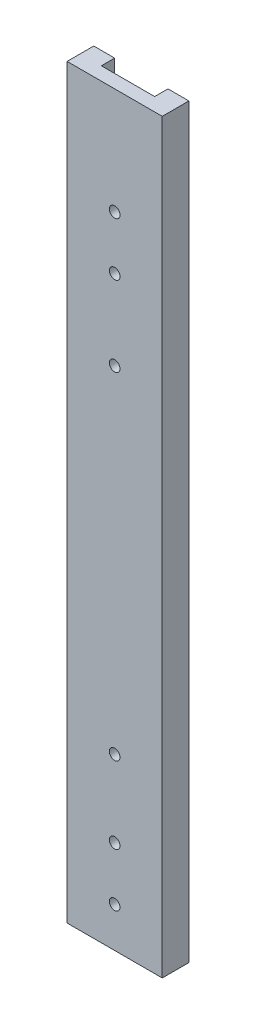
SolidWorks part; units mm, degrees
ref_plane "Front Plane" through (0, 0, 0) normal (0, 0, 1) x (1, 0, 0)
ref_plane "Top Plane" through (0, 0, 0) normal (0, 1, 0) x (1, 0, 0)
ref_plane "Right Plane" through (0, 0, 0) normal (1, 0, 0) x (0, 0, -1)
sketch "Sketch1" plane through (0, 0, 0) normal (0, 0, 1) x (1, 0, 0)
  line L1 (0, 0) -> (45.339, 0)
  line L2 (0, 0) -> (0, 355.6)
  line L3 (0, 355.6) -> (45.339, 355.6)
  line L4 (45.339, 0) -> (45.339, 355.6)
  dimension "D1" = 45.339
  dimension "D2" = 355.6
extrude "Boss-Extrude1" add sketch "Sketch1" along normal blind 12.7
sketch "Sketch2" plane through (0, 0, 0) normal (0, 0, -1) x (-1, 0, 0)
  line L0 (-45.339, 355.6) -> (0, 0) construction
  line L1 (-45.339, 355.6) -> (0, 355.6) construction
  line L2 (-9.9695, 0) -> (-35.3695, 0)
  line L3 (-9.9695, 0) -> (-9.9695, 355.6)
  line L4 (-9.9695, 355.6) -> (-35.3695, 355.6)
  line L5 (-35.3695, 0) -> (-35.3695, 355.6)
  line L6 (-9.9695, 0) -> (-35.3695, 355.6) construction
  line L7 (-9.9695, 355.6) -> (-35.3695, 0) construction
  point P4 (-22.6695, 177.8)
  dimension "D1" = 25.4
extrude "Cut-Extrude1" cut sketch "Sketch2" against normal blind 6.35
sketch "Sketch3" plane through (0, 0, 6.35) normal (0, 0, -1) x (-1, 0, 0)
  line L0 (-22.6695, 355.6) -> (-22.6695, 0) construction
  line L1 (-9.9695, 355.6) -> (-35.3695, 355.6) construction
  line L2 (-35.3695, 0) -> (-9.9695, 0) construction
  circle A0 centre (-22.6695, 19.05) radius 2.54
  circle A1 centre (-22.6695, 44.45) radius 2.54
  circle A2 centre (-22.6695, 304.8) radius 2.54
  circle A3 centre (-22.6695, 279.4) radius 2.54
  circle A4 centre (-22.6695, 241.3) radius 2.54
  circle A5 centre (-22.6695, 80.9625) radius 2.54
  dimension "D7" = 5.08
  dimension "D1" = 19.05
  dimension "D2" = 44.45
  dimension "D3" = 304.8
  dimension "D4" = 279.4
  dimension "D5" = 241.3
  dimension "D6" = 80.9625
extrude "Cut-Extrude2" cut sketch "Sketch3" against normal through all
